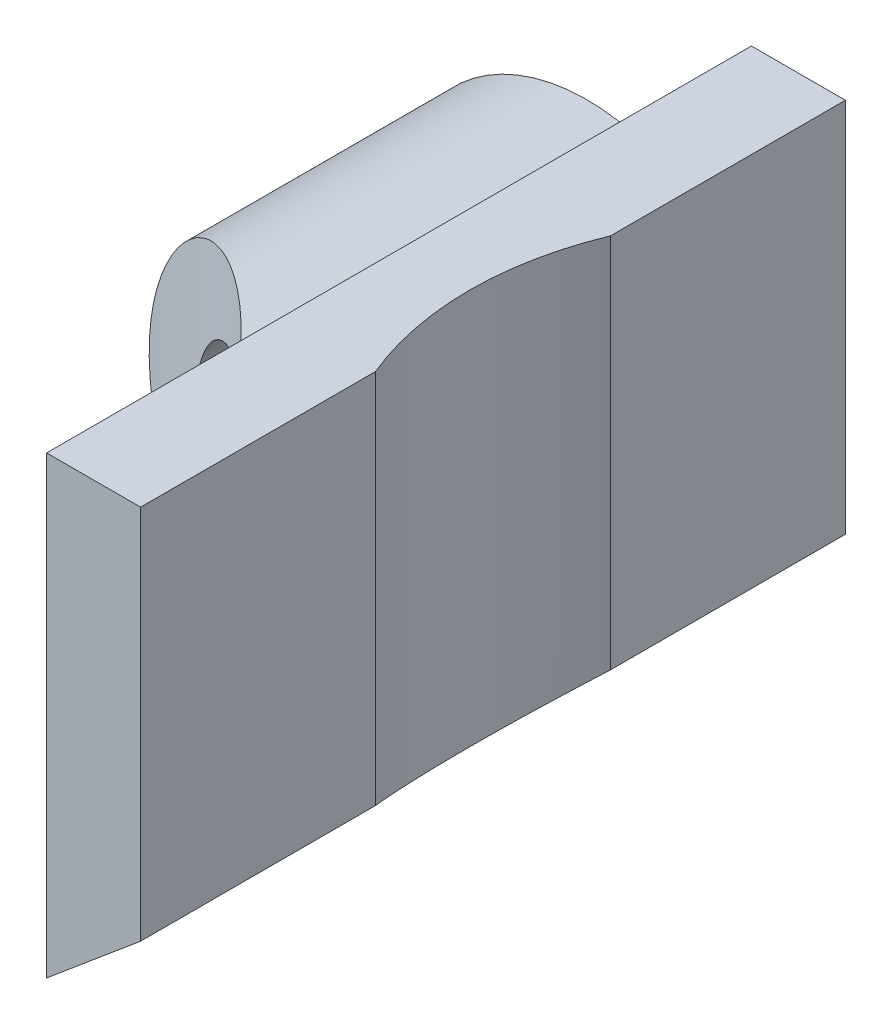
SolidWorks part; units mm, degrees
ref_plane "前基準面" through (0, 0, 0) normal (0, 0, 1) x (1, 0, 0)
ref_plane "上基準面" through (0, 0, 0) normal (0, 1, 0) x (1, 0, 0)
ref_plane "右基準面" through (0, 0, 0) normal (1, 0, 0) x (0, 0, -1)
sketch "草圖1" plane through (0, 0, 0) normal (0, 0, 1) x (1, 0, 0)
  line L0 (3.5, -2.9375) -> (5.5, -1.2593)
  line L1 (3.5, 6.7407) -> (5.5, 6.7407)
  line L2 (3.5, 6.7407) -> (3.5, 5.8095)
  line L4 (5.5, 6.7407) -> (5.5, -1.2593)
  line L5 (3.5, -2.9375) -> (2.715, -2.9375)
  circle A0 centre (0, 0) radius 2.5
  arc A1 (1, 3.873) -> (2.715, -2.9375) centre (0, 0) ccw
  arc A2 (3.5, 5.8095) -> (1, 3.873) centre (1.5, 5.8095) cw
  dimension "D1" = 8
  dimension "D2" = 5
  dimension "D8" = 2
  dimension "D3" = 3.5
  dimension "D4" = 2
  dimension "D5" = 8
  dimension "D6" = 50
  dimension "D7" = 4.5
extrude "填料-伸長1" add sketch "草圖1" along normal blind 15
sketch "草圖2" plane through (0, 6.7407, 0) normal (0, 1, 0) x (1, 0, 0)
  line L0 (5.5, -15) -> (3.5, -15)
  line L1 (-6.5, -5) -> (-4, -5)
  line L2 (-4, 0) -> (-4, -15) construction
  line L3 (-4, -5) -> (-4, 0)
  line L4 (-4, 0) -> (5.5, 0)
  line L5 (5.5, 0) -> (5.5, -5)
  line L6 (2.715, 0) -> (-4, 0) construction
  line L7 (11.5, -7.5) -> (5.5, -7.5) construction
  line L8 (5.5, -15) -> (5.5, 0) construction
  line L9 (5.5, 0) -> (3.5, 0) construction
  line L10 (5.5, -10) -> (5.5, -15)
  arc A0 (3.5, -15) -> (-6.5, -5) centre (-6.5, -15) ccw
  arc A1 (5.5, -5) -> (5.5, -10) centre (11.5, -7.5) ccw
  point P15 (-4, 4.2092)
  point P21 (4.5, 0)
  dimension "D2" = 13
  dimension "D3" = 0.5
  dimension "D1" = 5
extrude "除料-伸長1" cut sketch "草圖2" against normal through all flip side to cut
